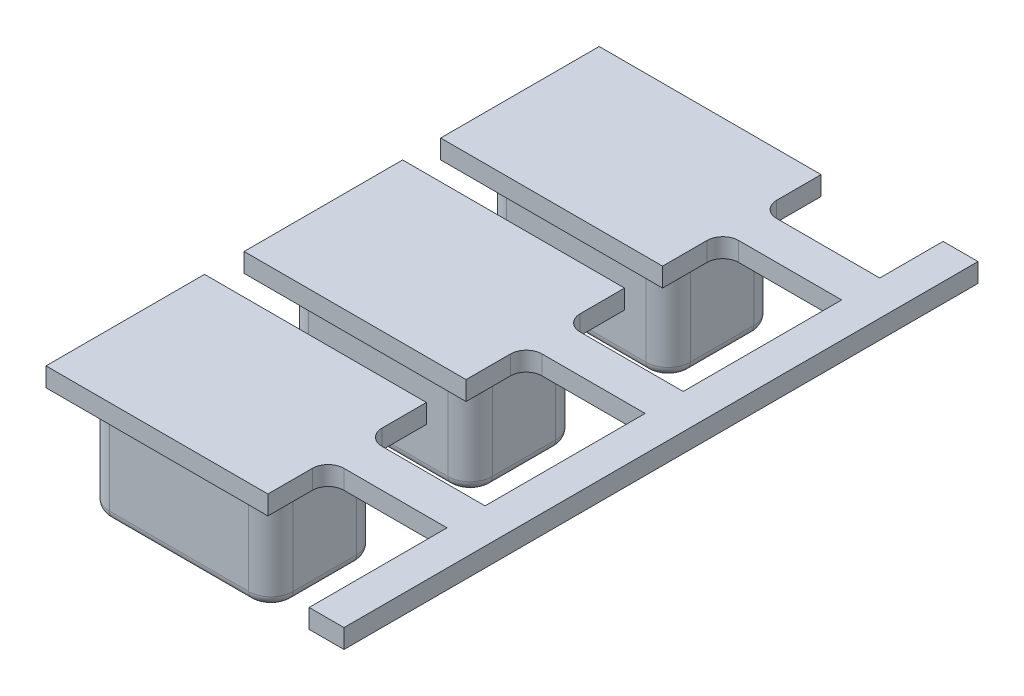
SolidWorks part; units mm, degrees
ref_plane "前视基准面" through (0, 0, 0) normal (0, 0, 1) x (1, 0, 0)
ref_plane "上视基准面" through (0, 0, 0) normal (0, 1, 0) x (1, 0, 0)
ref_plane "右视基准面" through (0, 0, 0) normal (1, 0, 0) x (0, 0, -1)
sketch "草图1" plane through (0, 0, 0) normal (0, 1, 0) x (1, 0, 0)
  line L0 (-2.2, 1.2454) -> (2.2, 1.2454)
  line L5 (-2.2, 7.5287) -> (2.2, 7.5287)
  line L6 (2.9, 6.8287) -> (2.9, 4.8287)
  line L7 (2.9, 0.5454) -> (2.9, -1.4546)
  line L8 (-2.2, -2.1546) -> (2.2, -2.1546)
  line L9 (-2.9, 0.5454) -> (-2.9, -1.4546)
  line L10 (-2.2, 4.1287) -> (2.2, 4.1287)
  line L11 (-2.9, 6.8287) -> (-2.9, 4.8287)
  line L12 (-2.2, 13.7759) -> (2.2, 13.7759)
  line L13 (2.9, 13.0759) -> (2.9, 11.0759)
  line L14 (-2.2, 10.3759) -> (2.2, 10.3759)
  line L15 (-2.9, 13.0759) -> (-2.9, 11.0759)
  arc A4 (2.2, 1.2454) -> (2.9, 0.5454) centre (2.2, 0.5454) cw
  arc A5 (2.2, -2.1546) -> (2.9, -1.4546) centre (2.2, -1.4546) ccw
  arc A6 (-2.9, -1.4546) -> (-2.2, -2.1546) centre (-2.2, -1.4546) ccw
  arc A7 (-2.2, 1.2454) -> (-2.9, 0.5454) centre (-2.2, 0.5454) ccw
  arc A8 (2.2, 7.5287) -> (2.9, 6.8287) centre (2.2, 6.8287) cw
  arc A9 (2.2, 4.1287) -> (2.9, 4.8287) centre (2.2, 4.8287) ccw
  arc A10 (-2.9, 4.8287) -> (-2.2, 4.1287) centre (-2.2, 4.8287) ccw
  arc A11 (-2.2, 7.5287) -> (-2.9, 6.8287) centre (-2.2, 6.8287) ccw
  arc A12 (2.2, 13.7759) -> (2.9, 13.0759) centre (2.2, 13.0759) cw
  arc A13 (2.2, 10.3759) -> (2.9, 11.0759) centre (2.2, 11.0759) ccw
  arc A14 (-2.9, 11.0759) -> (-2.2, 10.3759) centre (-2.2, 11.0759) ccw
  arc A15 (-2.2, 13.7759) -> (-2.9, 13.0759) centre (-2.2, 13.0759) ccw
  point P0 (0, 0)
  point P1 (-0.0497, 5.8287)
  point P15 (-0.0145, 11.6491)
  dimension "D1" = 3.4
  dimension "D2" = 5.8
extrude "凸台-拉伸1" add sketch "草图1" along normal blind 4
sketch "草图2" plane through (0, 4, 0) normal (0, 1, 0) x (1, 0, 0)
  line L1 (-3.4633, 14.5631) -> (3.5367, 14.5631)
  line L2 (-3.4633, 14.5631) -> (-3.4633, 9.5631)
  line L3 (-3.4633, 9.5631) -> (3.5367, 9.5631)
  line L4 (3.5367, 14.5631) -> (3.5367, 9.5631)
  line L5 (-3.4633, 8.3631) -> (3.5367, 8.3631)
  line L6 (-3.4633, 8.3631) -> (-3.4633, 3.3631)
  line L7 (-3.4633, 3.3631) -> (3.5367, 3.3631)
  line L8 (3.5367, 8.3631) -> (3.5367, 3.3631)
  line L9 (3.5367, 2.1131) -> (-3.4633, 2.1131)
  line L10 (3.5367, 2.1131) -> (3.5367, -2.8869)
  line L11 (3.5367, -2.8869) -> (-3.4633, -2.8869)
  line L12 (-3.4633, 2.1131) -> (-3.4633, -2.8869)
  dimension "D1" = 5
  dimension "D2" = 5
  dimension "D3" = 5
  dimension "D4" = 7
  dimension "D5" = 1.2
  dimension "D6" = 1.25
extrude "凸台-拉伸2" add sketch "草图2" against normal blind 0.6
sketch "草图3" plane through (0, 4, 0) normal (0, 1, 0) x (1, 0, 0)
  line L0 (3.5367, 9.5631) -> (3.5367, 14.5631) construction
  line L1 (3.5367, 12.6631) -> (8.3867, 12.6631)
  line L2 (3.5367, 12.6631) -> (3.5367, 11.4631)
  line L3 (3.5367, 11.4631) -> (8.3867, 11.4631)
  line L4 (8.3867, 12.6631) -> (8.3867, 11.4631)
  line L5 (3.5367, 3.3631) -> (3.5367, 8.3631) construction
  line L6 (3.5367, 6.4631) -> (8.3867, 6.4631)
  line L7 (3.5367, 6.4631) -> (3.5367, 5.2631)
  line L8 (3.5367, 5.2631) -> (8.3867, 5.2631)
  line L9 (8.3867, 6.4631) -> (8.3867, 5.2631)
  line L10 (3.5367, -2.8869) -> (3.5367, 2.1131) construction
  line L11 (3.5367, 0.2131) -> (8.3867, 0.2131)
  line L12 (3.5367, 0.2131) -> (3.5367, -0.9869)
  line L13 (3.5367, -0.9869) -> (8.3867, -0.9869)
  line L14 (8.3867, 0.2131) -> (8.3867, -0.9869)
  line L15 (-3.4633, 14.5631) -> (-3.4633, 9.5631) construction
  line L16 (-3.4633, 8.3631) -> (-3.4633, 3.3631) construction
  line L17 (-3.4633, 2.1131) -> (-3.4633, -2.8869) construction
  point P20 (-3.4633, 12.0631)
  point P21 (8.3867, 12.0631)
  point P24 (-3.4633, 5.8631)
  point P25 (8.3867, 5.8631)
  point P28 (-3.4633, -0.3869)
  point P29 (8.3867, -0.3869)
  dimension "D3" = 1.2
  dimension "D4" = 4.85
extrude "凸台-拉伸3" add sketch "草图3" against normal blind 0.6
sketch "草图4" plane through (0, 3.4, 0) normal (0, -1, 0) x (1, 0, 0)
  line L0 (3.5367, 0.9869) -> (8.3867, 0.9869) construction
  line L1 (8.3867, 0.9869) -> (7.3867, 0.9869)
  line L2 (8.3867, 0.9869) -> (8.3867, -12.6631)
  line L3 (8.3867, -12.6631) -> (7.3867, -12.6631)
  line L4 (7.3867, 0.9869) -> (7.3867, -12.6631)
  line L5 (8.3867, -12.6631) -> (3.5367, -12.6631) construction
  dimension "D1" = 1
extrude "凸台-拉伸4" add sketch "草图4" against normal blind 0.6
fillet "圆角1" radius 0.5 6 edges at (3.5367, 3.7, -12.6631) (3.5367, 3.7, -11.4631) (3.5367, 3.7, -5.2631) (3.5367, 3.7, -6.4631) (3.5367, 3.7, 0.9869) (3.5367, 3.7, -0.2131)
fillet "圆角2" radius 0.3 24 edges at (2.695, 0, -13.5709) (2.9, 0, -12.0759) (2.695, 0, -10.5809) (0, 0, -10.3759) (-2.695, 0, -10.5809) (-2.9, 0, -12.0759) (-2.695, 0, -13.5709) (2.695, 0, -7.3237) (2.9, 0, -5.8287) (2.695, 0, -4.3337) (0, 0, -4.1287) (-2.695, 0, -4.3337) (-2.9, 0, -5.8287) (-2.695, 0, -7.3237) (2.695, 0, -1.0404) (2.9, 0, 0.4546) (2.695, 0, 1.9496) (0, 0, 2.1546) (-2.695, 0, 1.9496) (-2.9, 0, 0.4546) (-2.695, 0, -1.0404) (0, 0, -13.7759) (0, 0, -7.5287) (0, 0, -1.2454)
sketch "草图5" plane through (0, 0, -12.6631) normal (0, 0, -1) x (-1, 0, 0)
  line L0 (-4.0367, 4) -> (-8.3867, 4) construction
  line L1 (-8.3867, 3.4) -> (-7.2867, 3.4)
  line L2 (-8.3867, 3.4) -> (-8.3867, 4)
  line L3 (-8.3867, 4) -> (-7.2867, 4)
  line L4 (-7.2867, 3.4) -> (-7.2867, 4)
  dimension "D1" = 1.1
extrude "凸台-拉伸5" add sketch "草图5" along normal blind 2 and the other way blind 18
